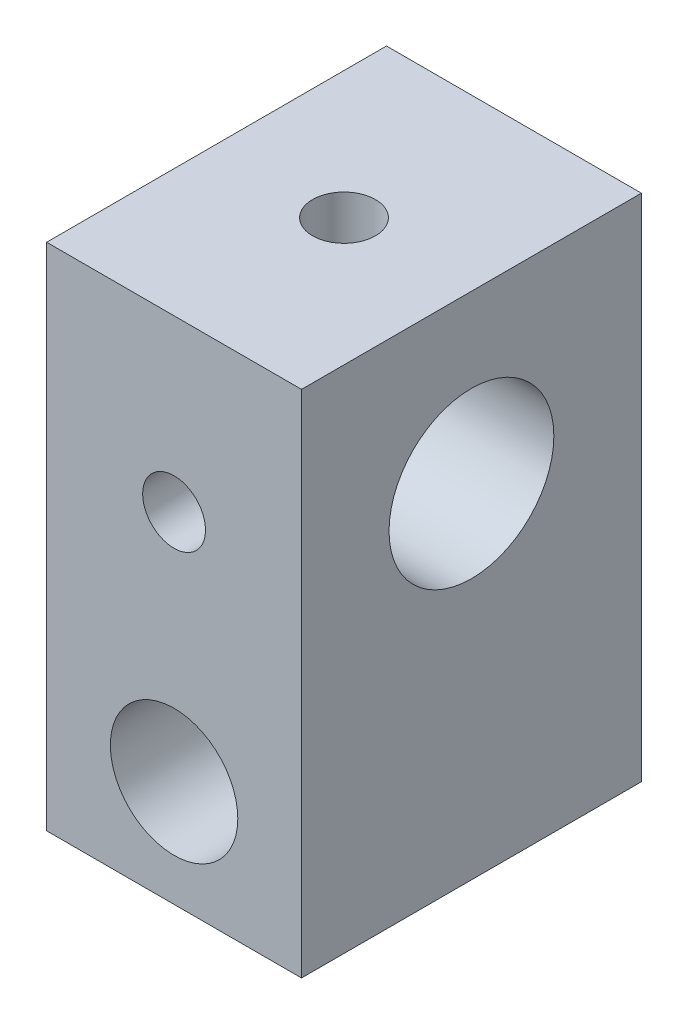
SolidWorks part; units mm, degrees
ref_plane "Front Plane" through (0, 0, 0) normal (0, 0, 1) x (1, 0, 0)
ref_plane "Top Plane" through (0, 0, 0) normal (0, 1, 0) x (1, 0, 0)
ref_plane "Right Plane" through (0, 0, 0) normal (1, 0, 0) x (0, 0, -1)
sketch "Sketch1" plane through (0, 0, 0) normal (0, 1, 0) x (1, 0, 0)
  line L1 (-9.525, -12.7) -> (9.525, -12.7)
  line L2 (-9.525, -12.7) -> (-9.525, 12.7)
  line L3 (-9.525, 12.7) -> (9.525, 12.7)
  line L4 (9.525, -12.7) -> (9.525, 12.7)
  line L5 (-9.525, -12.7) -> (9.525, 12.7) construction
  line L6 (-9.525, 12.7) -> (9.525, -12.7) construction
  point P0 (0, 0)
  dimension "D1" = 19.05
  dimension "D2" = 25.4
extrude "Boss-Extrude1" add sketch "Sketch1" along normal blind 38.1
sketch "Sketch2" plane through (0, 0, 12.7) normal (0, 0, 1) x (1, 0, 0)
  circle A0 centre (0, 7.9375) radius 4.7625
  dimension "D1" = 9.525
  dimension "D2" = 7.9375
extrude "Cut-Extrude1" cut sketch "Sketch2" against normal through all
sketch "Sketch3" plane through (9.525, 0, 0) normal (1, 0, 0) x (0, 0, -1)
  line L0 (-12.7, 38.1) -> (12.7, 38.1) construction
  circle A0 centre (0, 25.654) radius 6.1595
  dimension "D1" = 12.319
  dimension "D2" = 12.446
extrude "Cut-Extrude2" cut sketch "Sketch3" against normal through all
sketch "Sketch4" plane through (0, 38.1, 0) normal (0, 1, 0) x (1, 0, 0)
  line L0 (-9.525, 0) -> (9.525, 0) construction
  line L1 (-9.525, 12.7) -> (-9.525, -12.7) construction
  line L2 (9.525, -12.7) -> (9.525, 12.7) construction
  line L3 (0, -12.7) -> (0, 12.7) construction
  line L4 (-9.525, -12.7) -> (9.525, -12.7) construction
  line L5 (9.525, 12.7) -> (-9.525, 12.7) construction
  circle A0 centre (0, 0) radius 2.3495
extrude "Cut-Extrude3" cut sketch "Sketch4" against normal up to surface (6.7522 mm away)
sketch "Sketch5" plane through (0, 0, -12.7) normal (0, 0, -1) x (-1, 0, 0)
  line L0 (0, 38.1) -> (0, 0) construction
  line L1 (-9.525, 38.1) -> (9.525, 38.1) construction
  line L2 (-9.525, 0) -> (9.525, 0) construction
  circle A0 centre (0, 25.4) radius 2.3495
  dimension "D1" = 4.699
  dimension "D2" = 12.7
extrude "Cut-Extrude4" cut sketch "Sketch5" against normal through all
